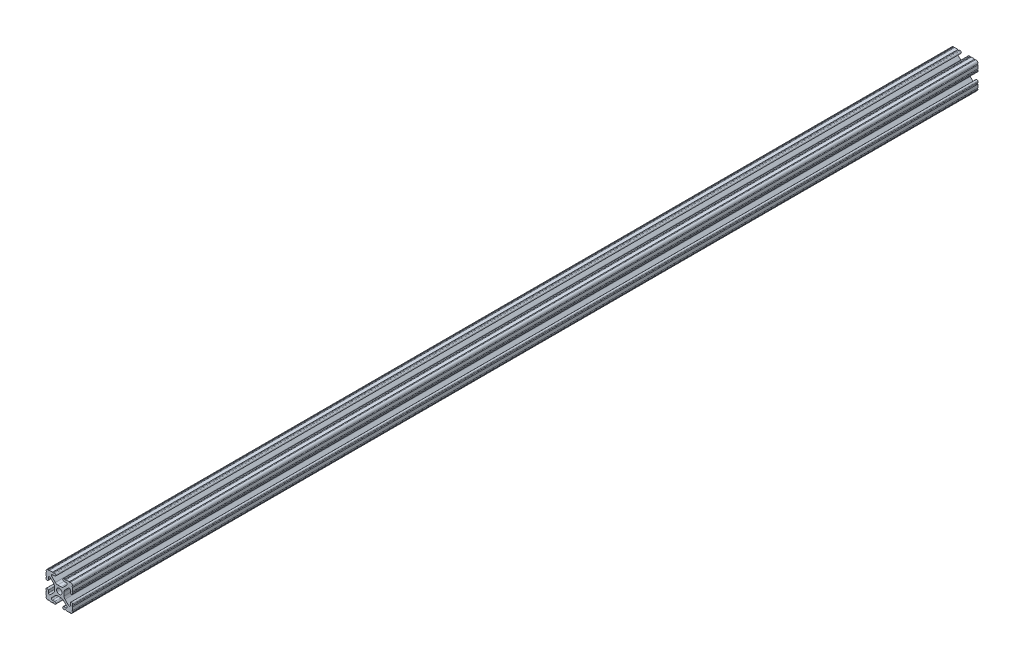
SolidWorks part; units mm, degrees
material "6061-T6 (SS)"
ref_plane "Front Plane" through (0, 0, 0) normal (0, 0, 1) x (1, 0, 0)
ref_plane "Top Plane" through (0, 0, 0) normal (0, 1, 0) x (1, 0, 0)
ref_plane "Right Plane" through (0, 0, 0) normal (1, 0, 0) x (0, 0, -1)
ref_plane "Plane1" through (0, 0, -450.85) normal (0, 0, -1) x (-1, 0, 0)
sketch "Sketch1" plane through (0, 0, -450.85) normal (0, 0, -1) x (-1, 0, 0)
  line L0 (12.7, -9.5504) -> (12.7, -6.3331)
  line L1 (12.7, -5.3171) -> (12.7, -4.3434)
  line L2 (10.4902, -4.3434) -> (10.4902, -6.4748)
  line L3 (8.7558, -7.1932) -> (5.4257, -3.8632)
  line L4 (4.4958, -1.6181) -> (4.4958, 1.6181)
  line L5 (5.4257, 3.8632) -> (8.7558, 7.1932)
  line L6 (10.4902, 6.4748) -> (10.4902, 4.3434)
  line L7 (12.7, 4.3434) -> (12.7, 5.3171)
  line L8 (12.7, 6.3331) -> (12.7, 9.5504)
  line L9 (9.5504, 12.7) -> (6.3331, 12.7)
  line L10 (5.3171, 12.7) -> (4.3434, 12.7)
  line L11 (4.3434, 10.4902) -> (6.4748, 10.4902)
  line L12 (7.1932, 8.7558) -> (3.8632, 5.4257)
  line L13 (1.6181, 4.4958) -> (-1.6181, 4.4958)
  line L14 (-3.8632, 5.4257) -> (-7.1932, 8.7558)
  line L15 (-6.4748, 10.4902) -> (-4.3434, 10.4902)
  line L16 (-4.3434, 12.7) -> (-5.3171, 12.7)
  line L17 (-6.3331, 12.7) -> (-9.5504, 12.7)
  line L18 (-12.7, 9.5504) -> (-12.7, 6.3331)
  line L19 (-12.7, 5.3171) -> (-12.7, 4.3434)
  line L20 (-10.4902, 4.3434) -> (-10.4902, 6.4748)
  line L21 (-8.7558, 7.1932) -> (-5.4257, 3.8632)
  line L22 (-4.4958, 1.6181) -> (-4.4958, -1.6181)
  line L23 (-5.4257, -3.8632) -> (-8.7558, -7.1932)
  line L24 (-10.4902, -6.4748) -> (-10.4902, -4.3434)
  line L25 (-12.7, -4.3434) -> (-12.7, -5.3171)
  line L26 (-12.7, -6.3331) -> (-12.7, -9.5504)
  line L27 (-9.5504, -12.7) -> (-6.3331, -12.7)
  line L28 (-5.3171, -12.7) -> (-4.3434, -12.7)
  line L29 (-4.3434, -10.4902) -> (-6.4748, -10.4902)
  line L30 (-7.1932, -8.7558) -> (-3.8632, -5.4257)
  line L31 (-1.6181, -4.4958) -> (1.6181, -4.4958)
  line L32 (3.8632, -5.4257) -> (7.1932, -8.7558)
  line L33 (6.4748, -10.4902) -> (4.3434, -10.4902)
  line L34 (4.3434, -12.7) -> (5.3171, -12.7)
  line L35 (6.3331, -12.7) -> (9.5504, -12.7)
  arc A0 (12.6998, -10.5664) -> (12.7, -9.5504) centre (12.7, -10.0584) cw
  arc A1 (12.7, -6.3331) -> (12.7, -5.3171) centre (12.7, -5.8251) cw
  arc A2 (12.7, -4.3434) -> (10.4902, -4.3434) centre (11.5951, -4.3434) ccw
  arc A3 (10.4902, -6.4748) -> (8.7558, -7.1932) centre (9.4742, -6.4748) cw
  arc A4 (5.4257, -3.8632) -> (4.4958, -1.6181) centre (7.6708, -1.6181) cw
  arc A5 (4.4958, 1.6181) -> (5.4257, 3.8632) centre (7.6708, 1.6181) cw
  arc A6 (8.7558, 7.1932) -> (10.4902, 6.4748) centre (9.4742, 6.4748) cw
  arc A7 (10.4902, 4.3434) -> (12.7, 4.3434) centre (11.5951, 4.3434) ccw
  arc A8 (12.7, 5.3171) -> (12.7, 6.3331) centre (12.7, 5.8251) cw
  arc A9 (12.7, 9.5504) -> (12.6998, 10.5664) centre (12.7, 10.0584) cw
  arc A10 (12.6998, 10.5664) -> (10.5664, 12.6998) centre (10.5918, 10.5918) ccw
  arc A11 (10.5664, 12.6998) -> (9.5504, 12.7) centre (10.0584, 12.7) cw
  arc A12 (6.3331, 12.7) -> (5.3171, 12.7) centre (5.8251, 12.7) cw
  arc A13 (4.3434, 12.7) -> (4.3434, 10.4902) centre (4.3434, 11.5951) ccw
  arc A14 (6.4748, 10.4902) -> (7.1932, 8.7558) centre (6.4748, 9.4742) cw
  arc A15 (3.8632, 5.4257) -> (1.6181, 4.4958) centre (1.6181, 7.6708) cw
  arc A16 (-1.6181, 4.4958) -> (-3.8632, 5.4257) centre (-1.6181, 7.6708) cw
  arc A17 (-7.1932, 8.7558) -> (-6.4748, 10.4902) centre (-6.4748, 9.4742) cw
  arc A18 (-4.3434, 10.4902) -> (-4.3434, 12.7) centre (-4.3434, 11.5951) ccw
  arc A19 (-5.3171, 12.7) -> (-6.3331, 12.7) centre (-5.8251, 12.7) cw
  arc A20 (-9.5504, 12.7) -> (-10.5664, 12.6998) centre (-10.0584, 12.7) cw
  arc A21 (-10.5664, 12.6998) -> (-12.6998, 10.5664) centre (-10.5918, 10.5918) ccw
  arc A22 (-12.6998, 10.5664) -> (-12.7, 9.5504) centre (-12.7, 10.0584) cw
  arc A23 (-12.7, 6.3331) -> (-12.7, 5.3171) centre (-12.7, 5.8251) cw
  arc A24 (-12.7, 4.3434) -> (-10.4902, 4.3434) centre (-11.5951, 4.3434) ccw
  arc A25 (-10.4902, 6.4748) -> (-8.7558, 7.1932) centre (-9.4742, 6.4748) cw
  arc A26 (-5.4257, 3.8632) -> (-4.4958, 1.6181) centre (-7.6708, 1.6181) cw
  arc A27 (-4.4958, -1.6181) -> (-5.4257, -3.8632) centre (-7.6708, -1.6181) cw
  arc A28 (-8.7558, -7.1932) -> (-10.4902, -6.4748) centre (-9.4742, -6.4748) cw
  arc A29 (-10.4902, -4.3434) -> (-12.7, -4.3434) centre (-11.5951, -4.3434) ccw
  arc A30 (-12.7, -5.3171) -> (-12.7, -6.3331) centre (-12.7, -5.8251) cw
  arc A31 (-12.7, -9.5504) -> (-12.6998, -10.5664) centre (-12.7, -10.0584) cw
  arc A32 (-12.6998, -10.5664) -> (-10.5664, -12.6998) centre (-10.5918, -10.5918) ccw
  arc A33 (-10.5664, -12.6998) -> (-9.5504, -12.7) centre (-10.0584, -12.7) cw
  arc A34 (-6.3331, -12.7) -> (-5.3171, -12.7) centre (-5.8251, -12.7) cw
  arc A35 (-4.3434, -12.7) -> (-4.3434, -10.4902) centre (-4.3434, -11.5951) ccw
  arc A36 (-6.4748, -10.4902) -> (-7.1932, -8.7558) centre (-6.4748, -9.4742) cw
  arc A37 (-3.8632, -5.4257) -> (-1.6181, -4.4958) centre (-1.6181, -7.6708) cw
  arc A38 (1.6181, -4.4958) -> (3.8632, -5.4257) centre (1.6181, -7.6708) cw
  arc A39 (7.1932, -8.7558) -> (6.4748, -10.4902) centre (6.4748, -9.4742) cw
  arc A40 (4.3434, -10.4902) -> (4.3434, -12.7) centre (4.3434, -11.5951) ccw
  arc A41 (5.3171, -12.7) -> (6.3331, -12.7) centre (5.8251, -12.7) cw
  arc A42 (9.5504, -12.7) -> (10.5664, -12.6998) centre (10.0584, -12.7) cw
  arc A43 (10.5664, -12.6998) -> (12.6998, -10.5664) centre (10.5918, -10.5918) ccw
  circle A44 centre (0, 0) radius 2.6035
extrude "Boss-Extrude1" add sketch "Sketch1" against normal blind 863.6
